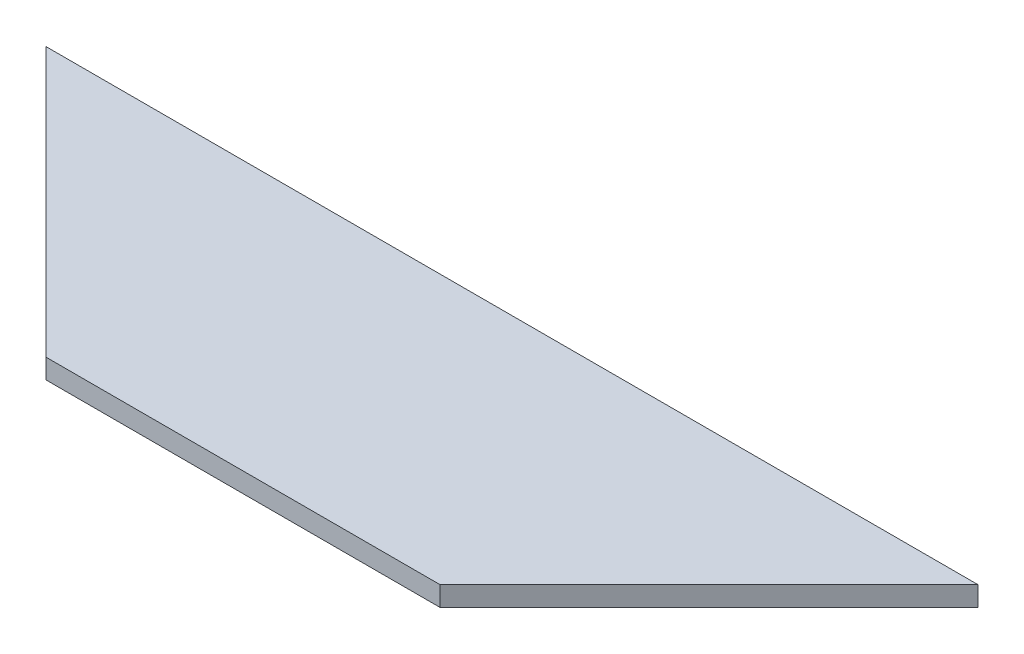
SolidWorks part; units mm, degrees
ref_plane "Front Plane" through (0, 0, 0) normal (0, 0, 1) x (1, 0, 0)
ref_plane "Top Plane" through (0, 0, 0) normal (0, 1, 0) x (1, 0, 0)
ref_plane "Right Plane" through (0, 0, 0) normal (1, 0, 0) x (0, 0, -1)
sketch "Sketch1" plane through (0, 0, 0) normal (0, 1, 0) x (1, 0, 0)
  line L0 (0, 0) -> (900, 0)
  line L1 (900, 0) -> (640.263, -259.737)
  line L2 (640.263, -259.737) -> (259.737, -259.737)
  line L3 (259.737, -259.737) -> (0, 0)
  dimension "D1" = 900
  dimension "D2" = 45
  dimension "D3" = 45
  dimension "D4" = 380.5259
extrude "Boss-Extrude1" add sketch "Sketch1" along normal blind 19.05
